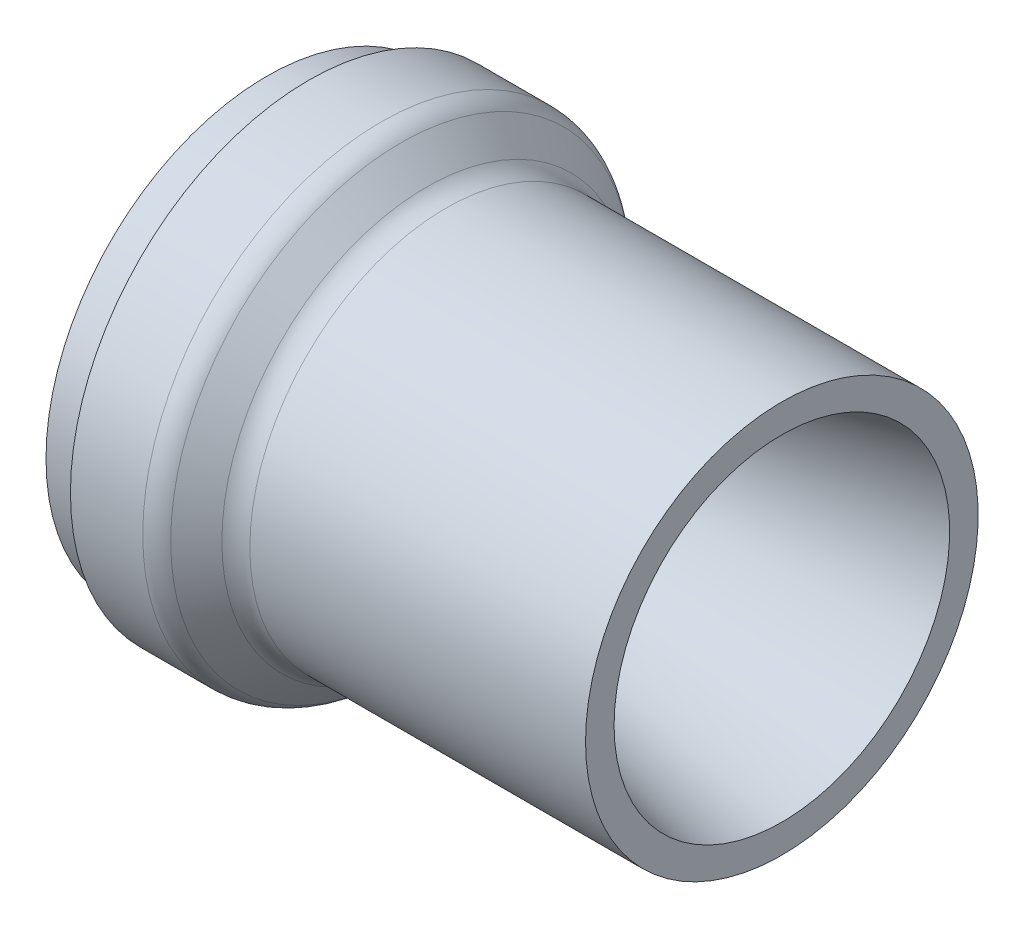
SolidWorks part; units mm, degrees
material "C (Graphite)"
ref_plane "Front Plane" through (0, 0, 0) normal (0, 0, 1) x (1, 0, 0)
ref_plane "Top Plane" through (0, 0, 0) normal (0, 1, 0) x (1, 0, 0)
ref_plane "Right Plane" through (0, 0, 0) normal (1, 0, 0) x (0, 0, -1)
sketch "Sketch1" plane through (0, 0, 0) normal (0, 0, 1) x (1, 0, 0)
  line L1 (116.9574, 12.446) -> (21.3593, 32.766)
  line L3 (0, 50.546) -> (76.2, 50.546) construction
  line L5 (15.0093, 32.766) -> (21.3593, 32.766)
  line L14 (0, 6.7691) -> (15.0093, 32.766)
  line L15 (30.4349, -1.6961) -> (36.2401, 4.1091)
  line L16 (40.7303, 5.969) -> (116.9574, 5.969)
  line L17 (116.9574, 5.969) -> (116.9574, 12.446)
  line L18 (25.9447, -3.556) -> (9.525, -3.556)
  line L19 (9.525, -3.556) -> (9.525, 0.4191)
  line L20 (0, 6.7691) -> (0, 0.4191)
  line L21 (0, 0.4191) -> (9.525, 0.4191)
  arc A2 (25.9447, -3.556) -> (30.4349, -1.6961) centre (25.9447, 2.794) ccw
  arc A3 (36.2401, 4.1091) -> (40.7303, 5.969) centre (40.7303, -0.381) cw
  point P1 (0, 0)
  point P2 (0, 0)
  point P13 (28.575, -3.556)
  point P16 (38.1, 5.969)
  dimension "D13" = 6.35
  dimension "D14" = 135
  dimension "D11" = 6.35
  dimension "D2" = 19.05
  dimension "D3" = 6.35
  dimension "D4" = 9.525
  dimension "D5" = 54.102
  dimension "D6" = 9.525
  dimension "D7" = 12
  dimension "D8" = 50.1269
  dimension "D9" = 17.78
  dimension "D10" = 60
  dimension "D12" = 38.1
revolve "Revolve1" add sketch "Sketch1" angle 360 about L3
